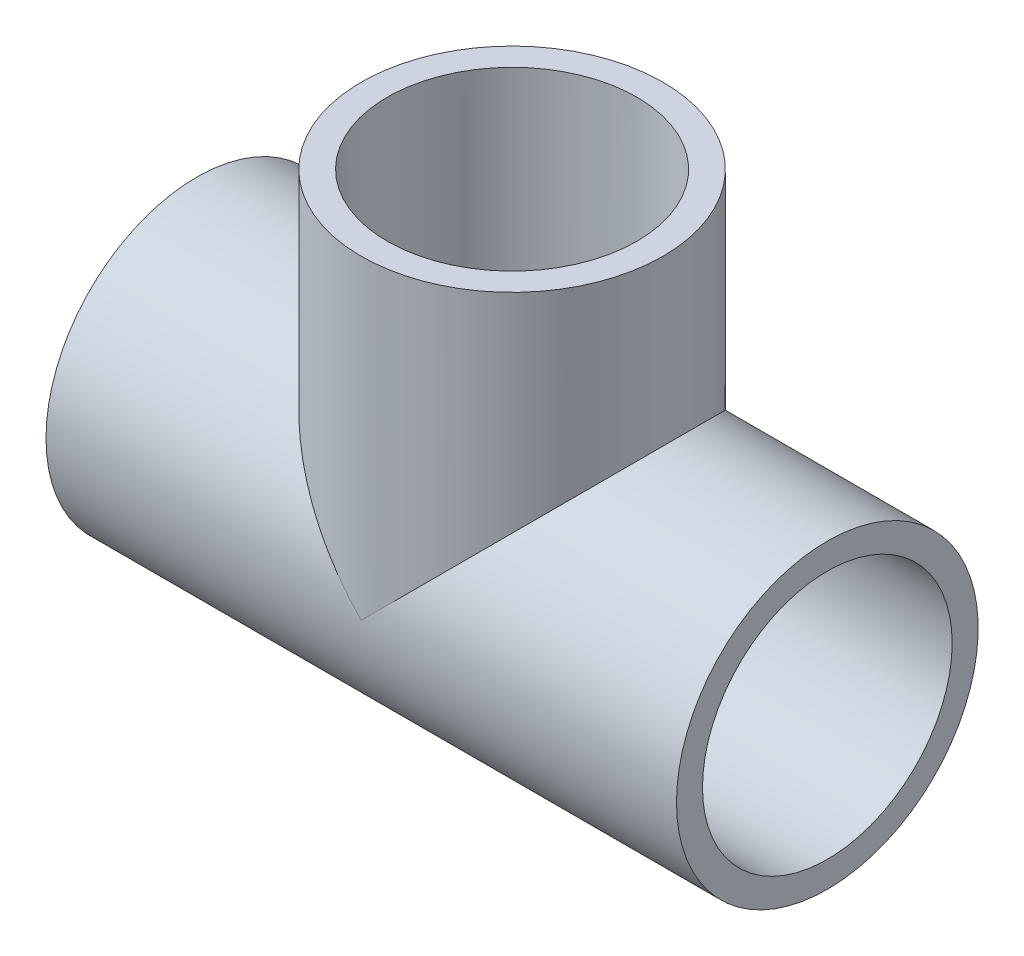
SolidWorks part; units mm, degrees
ref_plane "Front Plane" through (0, 0, 0) normal (0, 0, 1) x (1, 0, 0)
ref_plane "Top Plane" through (0, 0, 0) normal (0, 1, 0) x (1, 0, 0)
ref_plane "Right Plane" through (0, 0, 0) normal (1, 0, 0) x (0, 0, -1)
sketch "Sketch0" plane through (0, 0, 0) normal (0, 0, 1) x (1, 0, 0)
  line L0 (-42.4942, 0) -> (0, 0) construction
  line L1 (0, 0) -> (0, 42.4942) construction
  line L2 (-17.4752, 0) -> (0, 0) construction
  line L3 (0, 0) -> (0, 17.4752) construction
  line L4 (-42.4942, 20.3327) -> (-42.4942, -20.3327) construction
  line L5 (-17.4752, 16.637) -> (-42.4942, 16.8275) construction
  line L6 (-17.4752, 16.637) -> (-17.4752, -16.637) construction
  line L7 (-17.4752, -16.637) -> (-42.4942, -16.8275) construction
  line L8 (-42.4942, 16.8275) -> (-42.4942, -16.8275) construction
  line L9 (-20.3327, 42.4942) -> (20.3327, 42.4942) construction
  line L10 (-16.8275, 42.4942) -> (16.8275, 42.4942) construction
  line L11 (16.8275, 42.4942) -> (16.637, 17.4752) construction
  line L12 (16.637, 17.4752) -> (-16.637, 17.4752) construction
  line L13 (-16.637, 17.4752) -> (-16.8275, 42.4942) construction
  line L14 (-17.4752, 13.3223) -> (-17.4752, -13.3223) construction
  line L15 (-42.4942, 0) -> (-17.4752, 0) construction
  line L16 (0, 42.4942) -> (0, 17.4752) construction
  line L17 (0, 0) -> (17.4752, 0) construction
  line L18 (-13.3223, 17.4752) -> (13.3223, 17.4752) construction
  line L19 (17.4752, 0) -> (42.4942, 0) construction
  dimension "H" = 42.4942
  dimension "G" = 17.4752
  dimension "M" = 40.6654
  dimension "OD A" = 33.655
  dimension "OD B" = 33.274
  dimension "ID" = 26.6446
  dimension "H3" = 42.4942
sketch "Sketch1" plane through (0, 0, 0) normal (0, 0, 1) x (1, 0, 0)
  line L0 (-42.4942, 0) -> (0, 0) construction
  line L1 (-42.4942, 0) -> (0, 0) construction
  line L2 (0, 0) -> (0, -20.3327) construction
  line L3 (-42.4942, -20.3327) -> (-17.4752, -20.3327)
  line L4 (-42.4942, -20.3327) -> (-42.4942, -16.8275)
  line L5 (-42.4942, -16.8275) -> (-17.4752, -16.637)
  line L6 (-17.4752, -20.3327) -> (-17.4752, -16.637)
  line L7 (-17.4752, -20.3327) -> (0, -20.3327) construction
  line L8 (42.4942, -16.8275) -> (17.4752, -16.637)
  line L9 (42.4942, -20.3327) -> (42.4942, -16.8275)
  line L10 (17.4752, -20.3327) -> (17.4752, -16.637)
  line L11 (42.4942, -20.3327) -> (17.4752, -20.3327)
revolve "Revolve1" add sketch "Sketch1" angle 360 about L1
sketch "Sketch2" plane through (0, 0, 0) normal (0, 0, 1) x (1, 0, 0)
  line L0 (16.8275, 42.4942) -> (16.637, 17.4752)
  line L1 (16.637, 17.4752) -> (20.3327, 17.4752)
  line L2 (20.3327, 17.4752) -> (20.3327, 42.4942)
  line L3 (20.3327, 42.4942) -> (16.8275, 42.4942)
  line L4 (0, 0) -> (0, 42.4942) construction
  line L5 (0, 0) -> (0, 42.4942) construction
revolve "Revolve2" add sketch "Sketch2" angle 360 about L5
sketch "Sketch3" plane through (-17.4752, 0, 0) normal (1, 0, 0) x (0, 0, -1)
  circle A0 centre (0, 0) radius 13.3223
  circle A1 centre (0, 0) radius 20.3327
sketch "Sketch4" plane through (-17.4752, 0, 0) normal (1, 0, 0) x (0, 0, -1)
  circle A0 centre (0, 0) radius 20.3327 construction
  circle A1 centre (0, 0) radius 20.3327
extrude "Boss-Extrude1" add sketch "Sketch4" along normal up to vertex
sketch "Sketch5" plane through (0, 17.4752, 0) normal (0, -1, 0) x (1, 0, 0)
  circle A0 centre (0, 0) radius 20.3327 construction
  circle A1 centre (0, 0) radius 20.3327
extrude "Boss-Extrude2" add sketch "Sketch5" along normal up to vertex (17.4752 mm away) up to point (0, 0, 0)
sketch "Sketch6" plane through (0, 0, 0) normal (0, 0, 1) x (1, 0, 0)
  line L0 (-42.4942, -16.8275) -> (-17.4752, -16.637)
  line L1 (-17.4752, -16.637) -> (-17.4752, -13.3223)
  line L2 (-17.4752, -13.3223) -> (17.4752, -13.3223)
  line L3 (17.4752, -16.637) -> (17.4752, 12.9905) construction
  line L4 (0, -13.3223) -> (0, 0) construction
  line L5 (17.4752, -16.637) -> (17.4752, -13.3223)
  line L6 (42.4942, -16.8275) -> (42.4942, 16.8275) construction
  line L7 (42.4942, -20.3327) -> (42.4942, 20.3327) construction
  line L8 (42.4942, -16.8275) -> (42.4942, 0)
  line L9 (42.4942, 0) -> (-42.4942, 0)
  line L10 (-42.4942, 0) -> (-42.4942, -16.8275)
  line L11 (42.4942, -16.8275) -> (17.4752, -16.637)
revolve "Cut-Revolve1" cut sketch "Sketch6" angle 360 about L9
sketch "Sketch7" plane through (0, 0, 0) normal (0, 0, 1) x (1, 0, 0)
  line L0 (16.8275, 42.4942) -> (16.637, 17.4752)
  line L1 (16.637, 17.4752) -> (13.3223, 17.4752)
  line L2 (13.3223, 17.4752) -> (13.3223, 0)
  line L3 (0, 0) -> (17.4752, 0) construction
  line L4 (13.3223, 0) -> (0, 0)
  line L5 (0, 0) -> (0, 42.4942)
  line L6 (-20.3327, 42.4942) -> (20.3327, 42.4942) construction
  line L7 (0, 42.4942) -> (16.8275, 42.4942)
revolve "Cut-Revolve2" cut sketch "Sketch7" angle 360 about L5
